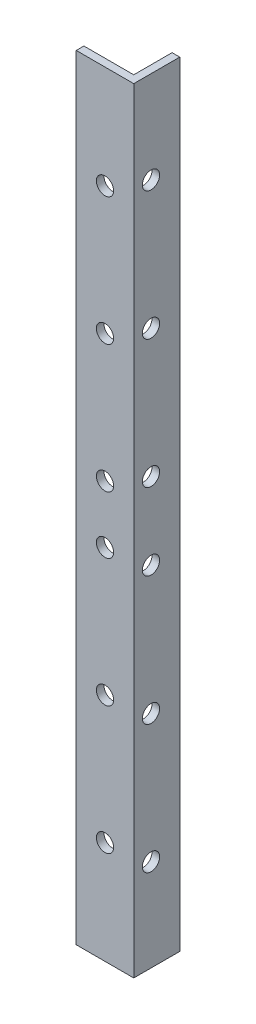
SolidWorks part; units mm, degrees
material "6061-T6 (SS)"
ref_plane "Alzado" through (0, 0, 0) normal (0, 0, 1) x (1, 0, 0)
ref_plane "Planta" through (0, 0, 0) normal (0, 1, 0) x (1, 0, 0)
ref_plane "Vista lateral" through (0, 0, 0) normal (1, 0, 0) x (0, 0, -1)
sketch "Sketch1" plane through (0, 0, 0) normal (0, 1, 0) x (1, 0, 0)
  line L0 (0, 0) -> (15, 0)
  line L1 (15, 0) -> (15, 12)
  line L2 (15, 12) -> (13, 12)
  line L3 (13, 12) -> (13, 2)
  line L4 (13, 2) -> (0, 2)
  line L5 (0, 2) -> (0, 0)
  dimension "D1" = 15
  dimension "D2" = 12
  dimension "D3" = 2
  dimension "D4" = 2
extrude "Boss-Extrude1" add sketch "Sketch1" along normal blind 202
sketch "Sketch2" plane through (0, 0, 0) normal (0, 0, 1) x (1, 0, 0)
  circle A0 centre (7.5, 175.1667) radius 2.25
  circle A1 centre (7.5, 141.8333) radius 2.25
  circle A2 centre (7.5, 108.5) radius 2.25
  circle A3 centre (7.5, 93.5) radius 2.25
  circle A4 centre (7.5, 60.1667) radius 2.25
  circle A5 centre (7.5, 26.8333) radius 2.25
  dimension "D1" = 4.5
extrude "Cut-Extrude1" cut sketch "Sketch2" against normal up to next
sketch "Sketch3" plane through (15, 0, 0) normal (1, 0, 0) x (0, 0, -1)
  circle A0 centre (4.5, 24) radius 2.25
  circle A1 centre (4.5, 57.5) radius 2.25
  circle A2 centre (4.5, 91) radius 2.25
  circle A3 centre (4.5, 111) radius 2.25
  circle A4 centre (4.5, 144.5) radius 2.25
  circle A5 centre (4.5, 178) radius 2.25
  dimension "D1" = 4.5
extrude "Cut-Extrude2" cut sketch "Sketch3" against normal up to next
